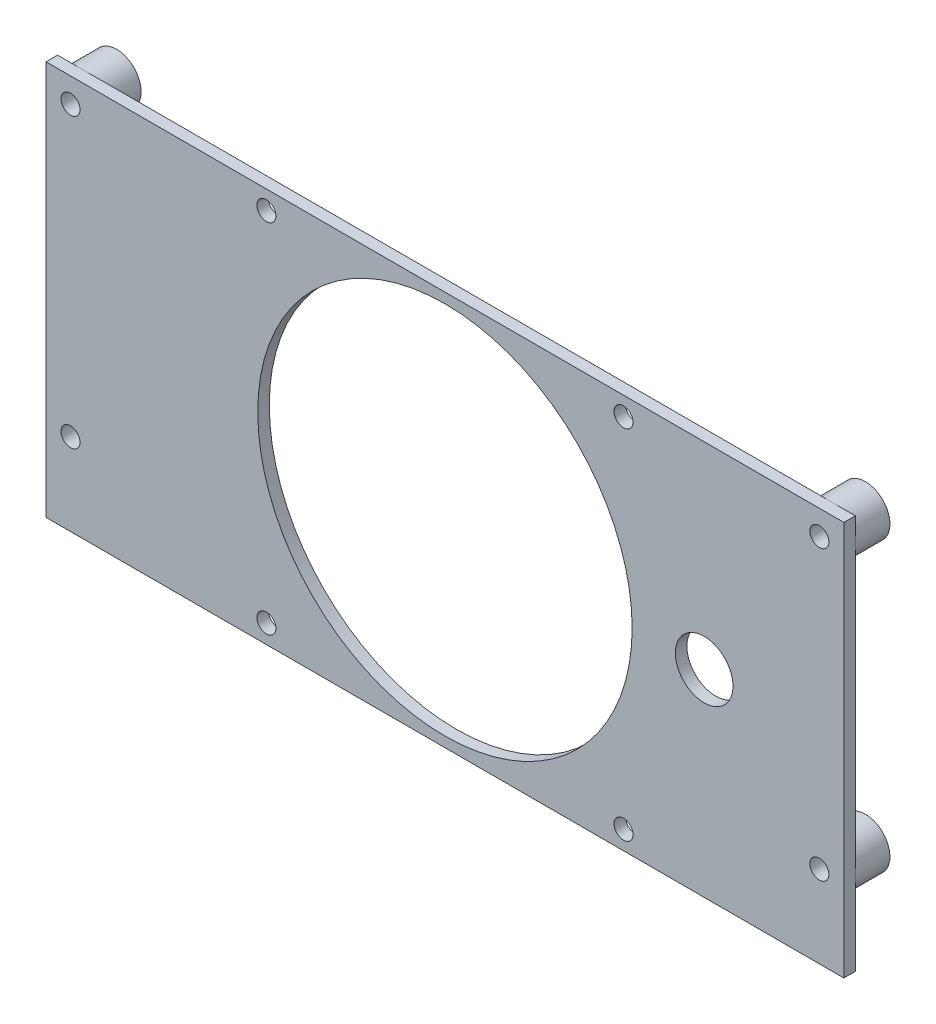
SolidWorks part; units mm, degrees
ref_plane "Plano frontal" through (0, 0, 0) normal (0, 0, 1) x (1, 0, 0)
ref_plane "Plano superior" through (0, 0, 0) normal (0, 1, 0) x (1, 0, 0)
ref_plane "Plano direito" through (0, 0, 0) normal (1, 0, 0) x (0, 0, -1)
sketch "Esboço1" plane through (0, 0, 0) normal (0, 0, 1) x (1, 0, 0)
  line L0 (0, 34.25) -> (0, 0) construction
  line L1 (-69.25, 34.25) -> (69.25, 34.25)
  line L2 (-69.25, 34.25) -> (-69.25, -34.25)
  line L3 (-69.25, -34.25) -> (69.25, -34.25)
  line L4 (69.25, 34.25) -> (69.25, -34.25)
  line L5 (-69.25, 34.25) -> (69.25, -34.25) construction
  line L6 (-69.25, -34.25) -> (69.25, 34.25) construction
  line L7 (0, 0) -> (-69.25, 0) construction
  circle A0 centre (-65, 30) radius 1.65
  circle A1 centre (-65, -20) radius 1.65
  circle A2 centre (65, -20) radius 1.65
  circle A3 centre (65, 30) radius 1.65
  circle A4 centre (0, 0) radius 32.5
  circle A5 centre (-31, 31) radius 1.65
  circle A6 centre (-31, -31) radius 1.65
  circle A7 centre (31, -31) radius 1.65
  circle A8 centre (31, 31) radius 1.65
  circle A9 centre (45, 0) radius 5
  point P0 (0, 0)
  dimension "D6" = 3.3
  dimension "D7" = 65
  dimension "D8" = 3.3
  dimension "D11" = 10
  dimension "D1" = 138.5
  dimension "D2" = 68.5
  dimension "D3" = 4.25
  dimension "D4" = 50
  dimension "D5" = 30
  dimension "D9" = 62
  dimension "D10" = 62
  dimension "D12" = 45
extrude "Ressalto-extrusão1" add sketch "Esboço1" along normal blind 2
sketch "Esboço2" plane through (0, 0, 0) normal (0, 0, -1) x (-1, 0, 0)
  line L0 (0, 0) -> (0, -34.25) construction
  line L1 (69.25, -34.25) -> (-69.25, -34.25) construction
  circle A0 centre (65, 30) radius 4.25
  circle A1 centre (65, 30) radius 1.65
  circle A2 centre (65, -20) radius 4.25
  circle A3 centre (65, -20) radius 1.65
  circle A4 centre (-65, -20) radius 1.65
  circle A5 centre (-65, -20) radius 4.25
  circle A6 centre (-65, 30) radius 1.65
  circle A7 centre (-65, 30) radius 4.25
extrude "Ressalto-extrusão2" add sketch "Esboço2" along normal blind 6
